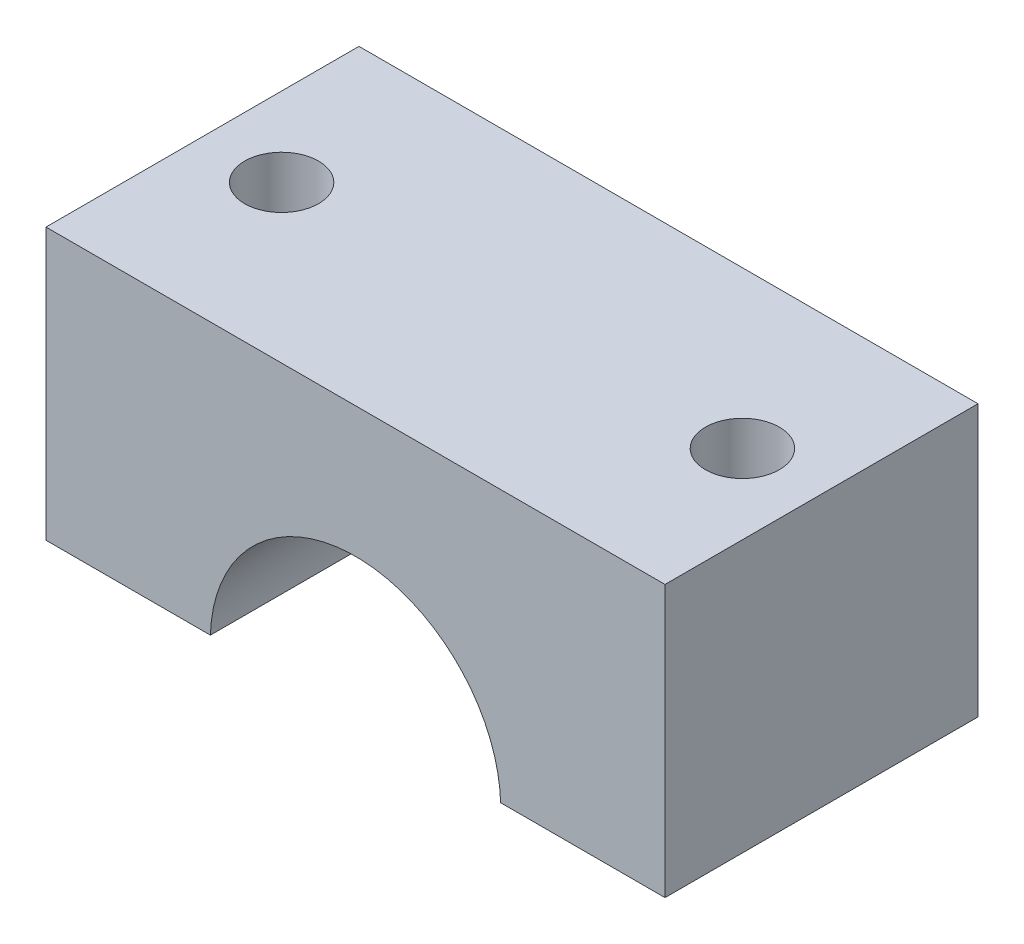
SolidWorks part; units mm, degrees
ref_plane "Plano frontal" through (0, 0, 0) normal (0, 0, 1) x (1, 0, 0)
ref_plane "Plano superior" through (0, 0, 0) normal (0, 1, 0) x (1, 0, 0)
ref_plane "Plano direito" through (0, 0, 0) normal (1, 0, 0) x (0, 0, -1)
sketch "Sketch1" plane through (0, 0, 0) normal (0, 0, 1) x (1, 0, 0)
  line L0 (-109.1298, 18.0519) -> (-144.7298, 18.0519) construction
  line L1 (-144.7298, 33.0519) -> (-73.5298, 33.0519)
  line L2 (-144.7298, 33.0519) -> (-144.7298, 1.3519)
  line L3 (-144.7298, 1.3519) -> (-73.5298, 1.3519)
  line L4 (-73.5298, 33.0519) -> (-73.5298, 1.3519)
  circle A0 centre (-109.1298, 1.3519) radius 16.7
  dimension "D2" = 33.4
  dimension "D1" = 71.2
  dimension "D3" = 15
extrude "Boss-Extrude1" add sketch "Sketch1" along normal blind 36 contours A0 L0 L2 L3 | L0 A0 L3 L4 L1 L2
sketch "Sketch2" plane through (0, 33.0519, 0) normal (0, 1, 0) x (1, 0, 0)
  line L0 (-144.7298, -18) -> (-135.6311, -18) construction
  line L1 (-144.7298, -36) -> (-144.7298, 0) construction
  line L2 (-73.5298, -18) -> (-82.6286, -18) construction
  line L3 (-73.5298, -36) -> (-73.5298, 0) construction
  circle A0 centre (-82.6286, -18) radius 4.25
  circle A1 centre (-135.6311, -18) radius 4.25
  dimension "D1" = 8.5
extrude "Cut-Extrude1" cut sketch "Sketch2" against normal through all
sketch "Sketch3" plane through (-144.7298, 0, 0) normal (-1, 0, 0) x (0, 0, 1)
  line L0 (36, 33.0519) -> (36, 1.3519) construction
  line L1 (0, 1.3519) -> (36, 1.3519)
  line L2 (0, 1.3519) -> (0, 1.8519)
  line L3 (0, 1.8519) -> (36, 1.8519)
  line L4 (36, 1.3519) -> (36, 1.8519)
  dimension "D1" = 0.5
extrude "Cut-Extrude2" cut sketch "Sketch3" against normal through all
